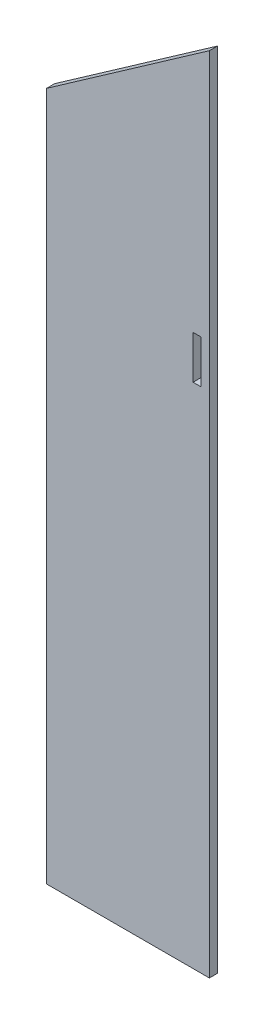
SolidWorks part; units mm, degrees
ref_plane "Front Plane" through (0, 0, 0) normal (0, 0, 1) x (1, 0, 0)
ref_plane "Top Plane" through (0, 0, 0) normal (0, 1, 0) x (1, 0, 0)
ref_plane "Right Plane" through (0, 0, 0) normal (1, 0, 0) x (0, 0, -1)
sketch "Sketch2" plane through (0, 0, 0) normal (0, 0, 1) x (1, 0, 0)
  line L0 (0, 0) -> (0, 571.8404) construction
  line L1 (-50, 422.98) -> (0, 422.98) construction
  line L2 (-50, 422.98) -> (-50, 0)
  line L3 (-50, 0) -> (50, 0)
  line L4 (50, 422.98) -> (50, 0)
  line L5 (-50, 422.98) -> (50, 493.0008)
  line L6 (50, 493.0008) -> (50, 422.98)
  line L7 (0, 422.98) -> (50, 422.98) construction
  dimension "D1" = 100
  dimension "D2" = 422.98
  dimension "D3" = 35
extrude "Boss-Extrude1" add sketch "Sketch2" along normal blind 5 contours L2 L3 L4 L6 L5
sketch "Sketch3" plane through (0, 0, 5) normal (0, 0, 1) x (1, 0, 0)
  line L0 (50, 493.0008) -> (50, 0) construction
  line L1 (40, 338.25) -> (45, 338.25)
  line L2 (40, 338.25) -> (40, 311.75)
  line L3 (40, 311.75) -> (45, 311.75)
  line L4 (45, 338.25) -> (45, 311.75)
  line L5 (-58.6102, 325) -> (109.2627, 325) construction
  line L6 (-50, 0) -> (50, 0) construction
  line L7 (-107.8206, 240) -> (237.1607, 240) construction
  line L8 (42, 253) -> (46, 253) construction
  line L9 (42, 253) -> (42, 227) construction
  line L10 (42, 227) -> (46, 227) construction
  line L11 (46, 253) -> (46, 227) construction
  point P6 (45, 325)
  dimension "D1" = 26.5
  dimension "D2" = 5
  dimension "D3" = 5
  dimension "D4" = 325
  dimension "D5" = 26
  dimension "D6" = 4
  dimension "D7" = 4
  dimension "D8" = 240
extrude "Cut-Extrude1" cut sketch "Sketch3" against normal up to next
